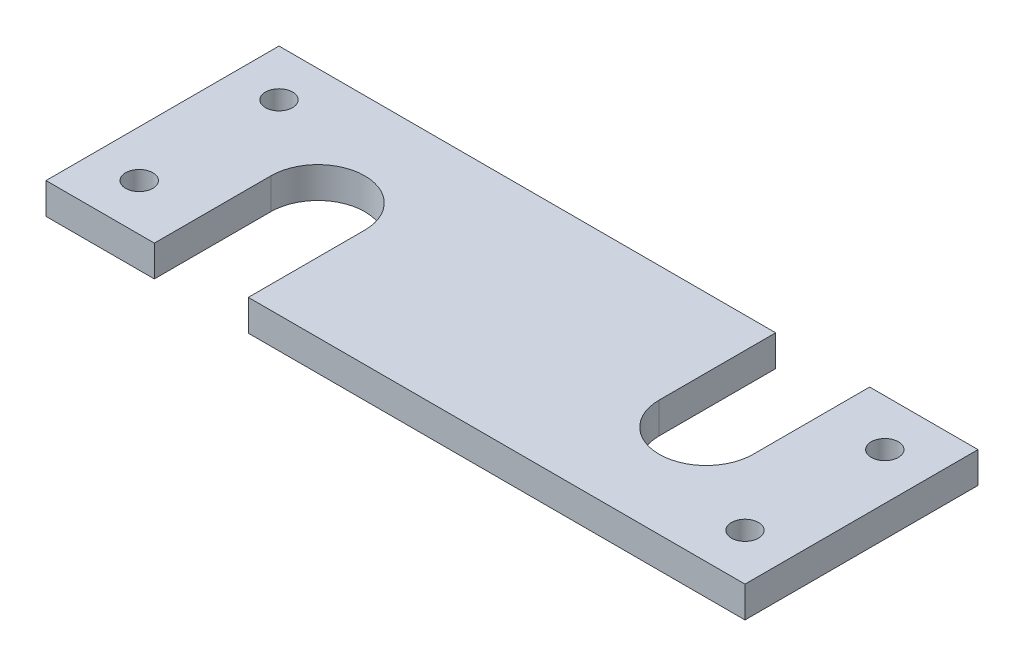
SolidWorks part; units mm, degrees
material "Balsa"
ref_plane "Front Plane" through (0, 0, 0) normal (0, 0, 1) x (1, 0, 0)
ref_plane "Top Plane" through (0, 0, 0) normal (0, 1, 0) x (1, 0, 0)
ref_plane "Right Plane" through (0, 0, 0) normal (1, 0, 0) x (0, 0, -1)
sketch "Sketch2" plane through (0, 0, 0) normal (0, 1, 0) x (1, 0, 0)
  line L0 (0, 0) -> (0, 30)
  line L1 (0, 0) -> (90, 0)
  line L2 (0, 30) -> (90, 30)
  line L3 (90, 0) -> (90, 30)
  dimension "D1" = 30
  dimension "D2" = 90
extrude "Boss-Extrude1" add sketch "Sketch2" along normal blind 4
sketch "Sketch3" plane through (0, 4, 0) normal (0, 1, 0) x (1, 0, 0)
  line L0 (13.95, 0) -> (26.05, 0)
  line L1 (0, 0) -> (90, 0) construction
  line L2 (26.05, 0) -> (26.05, 15)
  line L3 (0, 30) -> (0, 0) construction
  line L4 (13.95, 15) -> (13.95, 0)
  line L5 (63.95, 30) -> (63.95, 15)
  line L6 (90, 30) -> (0, 30) construction
  line L7 (90, 0) -> (90, 30) construction
  line L8 (76.05, 15) -> (76.05, 30)
  line L9 (76.05, 30) -> (63.95, 30)
  arc A0 (13.95, 15) -> (26.05, 15) centre (20, 15) cw
  arc A1 (63.95, 15) -> (76.05, 15) centre (70, 15) ccw
  circle A2 centre (6, 6) radius 1.75
  circle A3 centre (6, 24) radius 1.75
  circle A4 centre (84, 24) radius 1.75
  circle A5 centre (84, 6) radius 1.75
  dimension "D1" = 12.1
  dimension "D5" = 3.5
  dimension "D7" = 6
  dimension "D8" = 6
  dimension "D9" = 6
  dimension "D2" = 20
  dimension "D3" = 20
  dimension "D4" = 15
  dimension "D6" = 6
extrude "Cut-Extrude1" cut sketch "Sketch3" against normal through all
